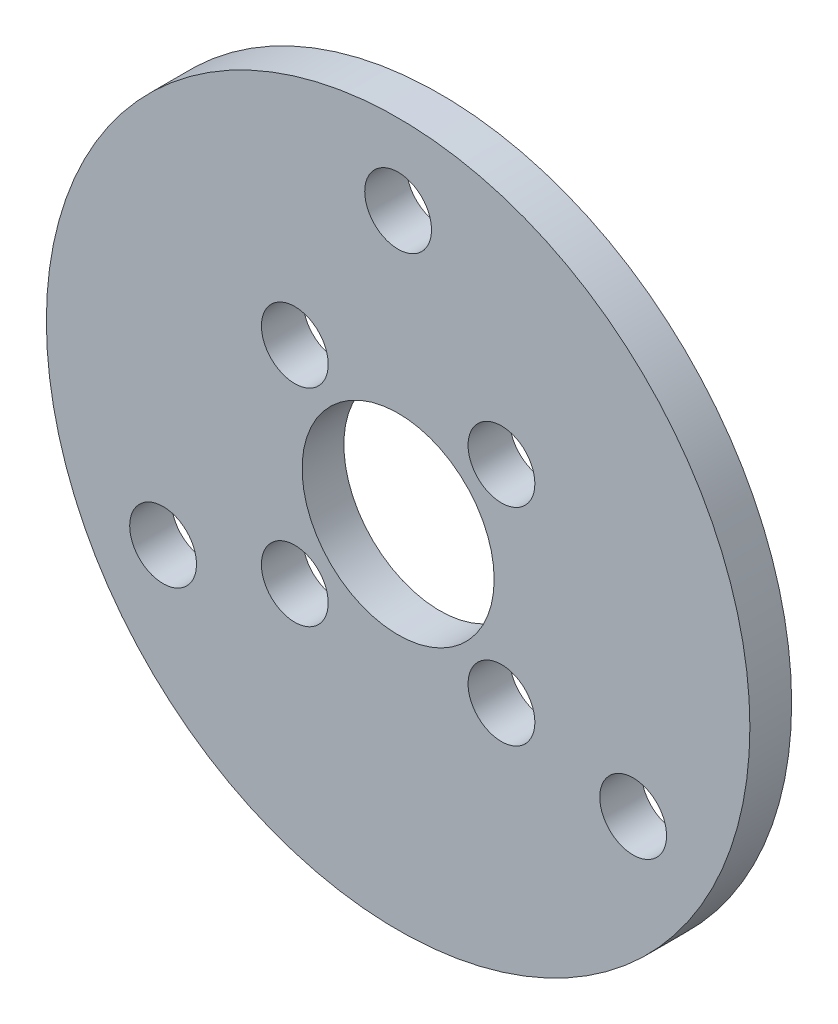
SolidWorks part; units mm, degrees
ref_plane "前视基准面" through (0, 0, 0) normal (0, 0, 1) x (1, 0, 0)
ref_plane "上视基准面" through (0, 0, 0) normal (0, 1, 0) x (1, 0, 0)
ref_plane "右视基准面" through (0, 0, 0) normal (1, 0, 0) x (0, 0, -1)
sketch "草图1" plane through (0, 0, 0) normal (0, 0, 1) x (1, 0, 0)
  line L0 (-22.2147, 0) -> (21.6095, 0) construction
  line L1 (0, 18.9405) -> (0, -18.5792) construction
  line L7 (15, -15) -> (-15, 15) construction
  line L8 (15, 15) -> (-15, -15) construction
  circle A0 centre (0, 0) radius 16.85
  circle A1 centre (0, 0) radius 4.6
  circle A2 centre (4.9497, 4.9497) radius 1.6
  circle A3 centre (4.9497, -4.9497) radius 1.6
  circle A4 centre (-4.9497, -4.9497) radius 1.6
  circle A5 centre (-4.9497, 4.9497) radius 1.6
  point P15 (0, 0)
  dimension "D1" = 33.7
  dimension "D2" = 9.2
  dimension "D3" = 3.2
  dimension "D4" = 7
  dimension "D6" = 30
  dimension "D7" = 30
  dimension "D5" = 4
extrude "凸台-拉伸1" add sketch "草图1" along normal blind 2 contours A0 A5 A4 A3 A2 A1
sketch "草图2" plane through (0, 0, 0) normal (0, 0, -1) x (-1, 0, 0)
  line L0 (-4.9497, 4.9497) -> (4.9497, 4.9497) construction
  line L1 (0, -5.8738) -> (0, 15.7733)
  line L2 (0, 0) -> (11.2583, -6.5) construction
  line L3 (0, 0) -> (-11.2583, -6.5) construction
  circle A0 centre (0, 13) radius 1.6
  circle A1 centre (-4.9497, 4.9497) radius 1.6 construction
  circle A2 centre (-4.9497, 4.9497) radius 1.6 construction
  circle A3 centre (4.9497, 4.9497) radius 1.6 construction
  circle A4 centre (4.9497, 4.9497) radius 1.6 construction
  circle A5 centre (11.2583, -6.5) radius 1.6
  circle A6 centre (-11.2583, -6.5) radius 1.6
  point P12 (0, 4.9497)
  point P19 (0, 0)
  dimension "D1" = 3.2
  dimension "D2" = 13
  dimension "D4" = 120
  dimension "D5" = 120
  dimension "D3" = 3
extrude "切除-拉伸1" cut sketch "草图2" against normal through all contours L1 A0 | L1 A0 | A6 | A5
